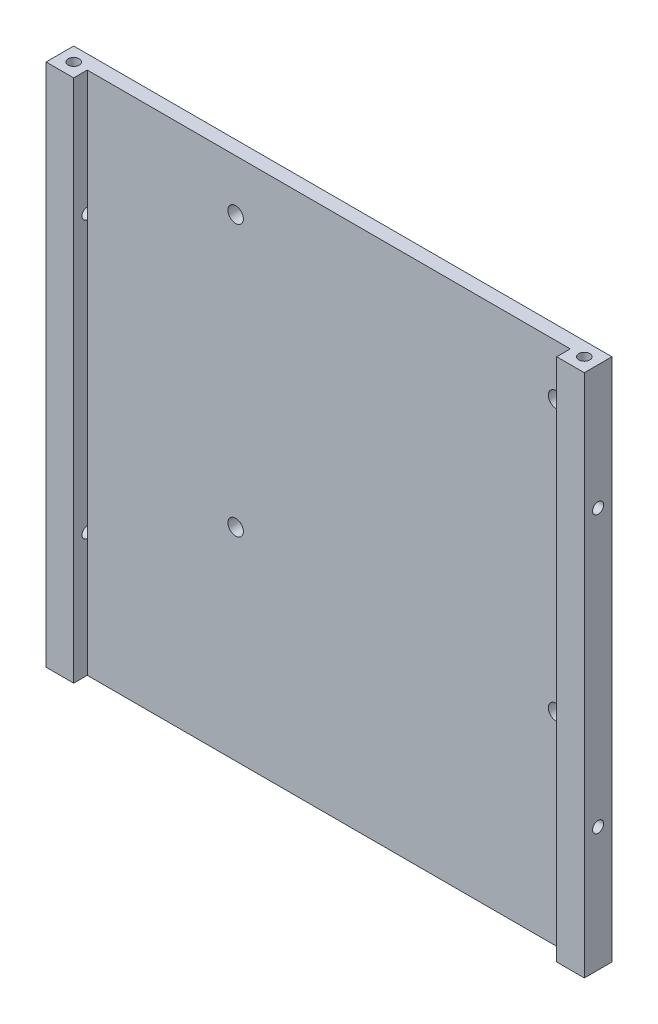
SolidWorks part; units mm, degrees
material "6061 Alloy"
ref_plane "Front Plane" through (0, 0, 0) normal (0, 0, 1) x (1, 0, 0)
ref_plane "Top Plane" through (0, 0, 0) normal (0, 1, 0) x (1, 0, 0)
ref_plane "Right Plane" through (0, 0, 0) normal (1, 0, 0) x (0, 0, -1)
sketch "Sketch1" plane through (0, 0, 0) normal (0, 0, 1) x (1, 0, 0)
  line L1 (0, 0) -> (97.46, 0)
  line L2 (0, 0) -> (0, 97.46)
  line L3 (0, 97.46) -> (97.46, 97.46)
  line L4 (97.46, 0) -> (97.46, 97.46)
extrude "Boss-Extrude1" add sketch "Sketch1" along normal blind 1.27 contours L2 L3 L4 L1
sketch "Sketch3" plane through (0, 0, 1.27) normal (0, 0, 1) x (1, 0, 0)
  line L0 (0, 0) -> (0, 5) construction
  line L1 (0, 5) -> (65, 5)
  line L2 (65, 5) -> (65, 10.1725)
  line L3 (65, 10.1725) -> (0, 10.1725)
  line L4 (0, 25) -> (65, 25)
  line L5 (65, 25) -> (65, 30.1725)
  line L6 (65, 30.1725) -> (0, 30.1725)
  line L7 (0, 65) -> (0, 70.1725)
  line L8 (0, 45) -> (65, 45)
  line L9 (65, 45) -> (65, 50.1725)
  line L10 (65, 50.1725) -> (0, 50.1725)
  line L11 (0, 50.1725) -> (0, 45)
  line L12 (0, 65) -> (65, 65)
  line L13 (65, 65) -> (65, 70.1725)
  line L14 (65, 70.1725) -> (0, 70.1725)
  line L15 (0, 0) -> (5, 0)
  line L16 (0, 5) -> (0, 10.1725)
  line L17 (0, 25) -> (0, 30.1725)
  line L18 (0, 20) -> (0, 25) construction
  line L19 (0, 40) -> (0, 45) construction
  line L20 (0, 60) -> (0, 65) construction
  line L21 (5, 0) -> (5, 97.46)
  line L22 (5, 97.46) -> (0, 97.46)
  line L23 (0, 97.46) -> (0, 0)
  line L24 (97.46, 0) -> (92.46, 0)
  line L25 (97.46, 0) -> (97.46, 97.46)
  line L26 (97.46, 97.46) -> (92.46, 97.46)
  line L27 (92.46, 97.46) -> (92.46, 0)
  line L28 (0, 97.46) -> (0, 92.46)
  line L29 (92.46, 97.46) -> (92.46, 92.46)
  line L30 (92.46, 5) -> (92.46, 0)
  line L31 (92.46, 5) -> (97.46, 5)
  line L32 (92.46, 92.46) -> (97.46, 92.46)
  line L33 (0, 92.46) -> (5, 92.46)
  point P8 (97.46, 0)
  line M4 (0, 0) -> (97.46, 0)
  line M5 (97.46, 0) -> (97.46, 97.46)
  line M6 (97.46, 97.46) -> (0, 97.46)
  line M7 (0, 97.46) -> (0, 0)
  dimension "D1" = 4
extrude "Boss-Extrude2" add sketch "Sketch3" along normal blind 3.73 contours L14 L21 M6 M7 | L12 L21 L14 M7 | L10 L21 L12 M7 | L8 L21 L10 M7 | L6 L21 L8 M7 | L4 L21 L6 M7 | L3 L21 L4 M7 | L27 M6 M4 M5 | L1 L21 L3 M7 | L31 L27 M4 M5 | L27 L32 M5 M6 | L21 L1 M4 M7 | L33 L21 M7 M6
sketch "Sketch4" plane through (0, 0, 0) normal (0, -1, 0) x (1, 0, 0)
  line L0 (97.46, 0) -> (94.96, 0) construction
  line L1 (97.46, 0) -> (97.46, 2.5)
  circle A0 centre (94.96, 2.5) radius 1
sketch "Sketch5" plane through (0, 0, 0) normal (0, -1, 0) x (1, 0, 0)
  circle A0 centre (2.5, 2.5) radius 1
sketch "Sketch6" plane through (0, 97.46, 0) normal (0, 1, 0) x (-1, 0, 0)
  line L0 (-97.46, 0) -> (-94.96, 0) construction
  line L1 (-94.96, 0) -> (-94.96, 2.5) construction
  circle A0 centre (-94.96, 2.5) radius 1
sketch "Sketch7" plane through (0, 97.46, 0) normal (0, 1, 0) x (-1, 0, 0)
  circle A0 centre (-2.5, 2.5) radius 1
extrude "Cut-Extrude2" cut sketch "Sketch7" against normal blind 5
extrude "Cut-Extrude3" cut sketch "Sketch6" against normal blind 5 contours A0
extrude "Cut-Extrude4" cut sketch "Sketch4" against normal blind 5 contours A0
extrude "Cut-Extrude5" cut sketch "Sketch5" against normal blind 5 contours A0
sketch "Sketch9" plane through (97.46, 0, 0) normal (1, 0, 0) x (0, 0, -1)
  line L3 (-2.5, 23.73) -> (-2.5, 73.73) construction
  line L5 (0, 48.73) -> (-2.5, 48.73) construction
  line L6 (0, 97.46) -> (0, 0) construction
  circle A2 centre (-2.5, 73.73) radius 1
  circle A3 centre (-2.5, 23.73) radius 1
sketch "Sketch10" plane through (0, 0, 0) normal (-1, 0, 0) x (0, 0, 1)
  line L0 (2.5, 73.73) -> (2.5, 23.73) construction
  line L1 (0, 48.73) -> (2.5, 48.73) construction
  line L2 (0, 0) -> (0, 97.46) construction
  circle A0 centre (2.5, 23.73) radius 1
  circle A1 centre (2.5, 73.73) radius 1
extrude "Cut-Extrude7" cut sketch "Sketch10" against normal up to next
extrude "Cut-Extrude8" cut sketch "Sketch9" against normal up to next
sketch "Sketch11" plane through (0, 0, 0) normal (0, -1, 0) x (-1, 0, 0)
  line L0 (-92.46, -5) -> (-97.46, -5)
  line L1 (-97.46, -5) -> (-97.46, 0)
  line L2 (-97.46, 0) -> (0, 0)
  line L3 (0, 0) -> (0, -5)
  line L4 (0, -5) -> (-5, -5)
  line L5 (-5, -5) -> (-5, -1.27)
  line L6 (-5, -1.27) -> (-92.46, -1.27)
  line L7 (-92.46, -1.27) -> (-92.46, -5)
extrude "Cut-Extrude9" cut sketch "Sketch11" against normal blind 1.27
sketch "Sketch12" plane through (0, 97.46, 0) normal (0, 1, 0) x (1, 0, 0)
  line L0 (92.46, -1.27) -> (92.46, -5)
  line L1 (92.46, -5) -> (97.46, -5)
  line L2 (97.46, -5) -> (97.46, 0)
  line L3 (97.46, 0) -> (0, 0)
  line L4 (0, 0) -> (0, -5)
  line L5 (0, -5) -> (5, -5)
  line L6 (5, -5) -> (5, -1.27)
  line L7 (5, -1.27) -> (92.46, -1.27)
extrude "Cut-Extrude10" cut sketch "Sketch12" against normal blind 1.27
sketch "Sketch13" plane through (0, 0, 1.27) normal (0, 0, 1) x (1, 0, 0)
  line L0 (92.46, 96.19) -> (92.46, 1.27)
  line L1 (92.46, 1.27) -> (5, 1.27)
  line L2 (5, 1.27) -> (5, 96.19)
  line L3 (5, 96.19) -> (92.46, 96.19)
extrude "Boss-Extrude3" add sketch "Sketch13" along normal blind 1.27
sketch "Sketch8" plane through (0, 0, 0) normal (0, 0, -1) x (-1, 0, 0)
  line L0 (-31.8641, 37.9434) -> (-31.8641, 26.9165) construction
  line L1 (-31.8641, 86.9434) -> (-31.8641, 37.9434) construction
  line L2 (-31.8641, 37.9434) -> (-25.1384, 37.9434) construction
  line L3 (-25.1384, 31.9165) -> (-25.1384, 26.9165) construction
  line L4 (-25.1384, 26.9165) -> (-30.1384, 26.9165) construction
  line L5 (-31.8641, 26.9165) -> (-25.1384, 26.9165) construction
  line L6 (-25.1384, 26.9165) -> (-25.1384, 37.9434) construction
  circle A0 centre (-31.8641, 37.9434) radius 1.4
  circle A1 centre (-89.8741, 86.9534) radius 1.4
  circle A2 centre (-31.8641, 86.9534) radius 1.4
  circle A3 centre (-89.8741, 37.9434) radius 1.4
extrude "Cut-Extrude6" cut sketch "Sketch8" against normal blind 10
